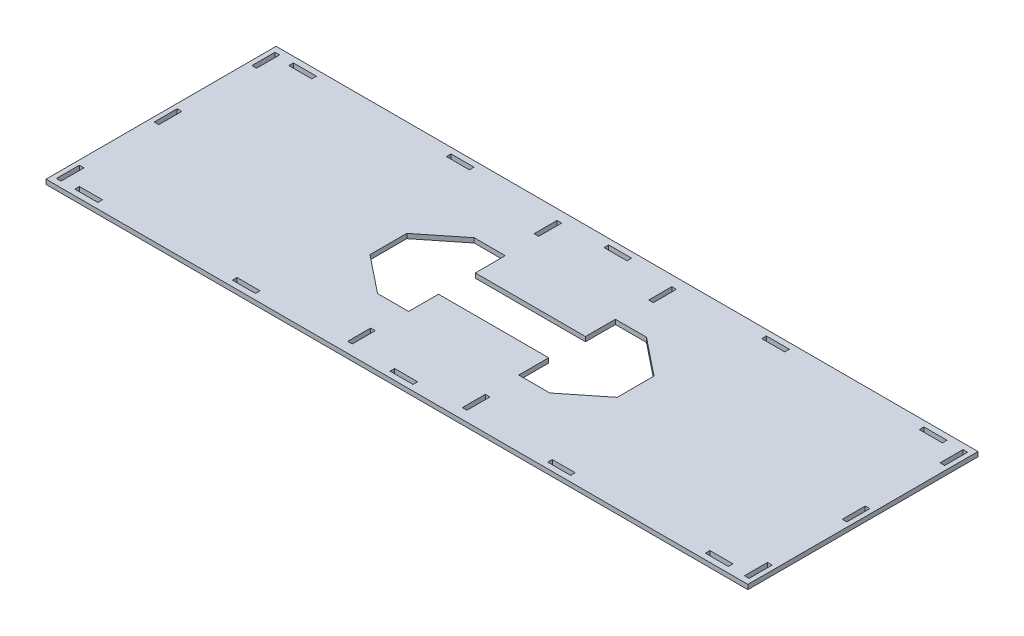
SolidWorks part; units mm, degrees
ref_plane "Front Plane" through (0, 0, 0) normal (0, 0, 1) x (1, 0, 0)
ref_plane "Top Plane" through (0, 0, 0) normal (0, 1, 0) x (1, 0, 0)
ref_plane "Right Plane" through (0, 0, 0) normal (1, 0, 0) x (0, 0, -1)
sketch "Sketch1" plane through (0, 0, 0) normal (0, 1, 0) x (1, 0, 0)
  line L0 (0, 0) -> (0, 189.2154) construction
  line L1 (-305, 100) -> (-305, -100)
  line L2 (-305, -100) -> (305, -100)
  line L4 (-305, 100) -> (305, 100)
  line L6 (-330, -100) -> (330, 100) construction
  line L7 (-330, 100) -> (330, -100) construction
  line L60 (-301, -95) -> (-301, -75)
  line L61 (-301, -95) -> (326, -95) construction
  line L62 (-301, -95) -> (-301, 95) construction
  line L63 (-301, 95) -> (326, 95) construction
  line L65 (-301, -95) -> (326, 95) construction
  line L66 (-301, 95) -> (326, -95) construction
  line L67 (-301, -95) -> (-297, -95)
  line L68 (-301, 95) -> (-297, 95)
  line L69 (-301, -75) -> (-297, -75)
  line L71 (-421.8057, 0) -> (404.5887, 0) construction
  line L72 (-301, 75) -> (-301, 95)
  line L73 (-301, -10) -> (-297, -10)
  line L76 (-301, -10) -> (-301, 10)
  line L77 (-301, 10) -> (-297, 10)
  line L78 (-297, 10) -> (-297, -10)
  line L79 (-301, 75) -> (-297, 75)
  line L91 (-265, 95) -> (-285, 95)
  line L93 (-265, 95) -> (-265, 91)
  line L94 (-148, 95) -> (-128, 95)
  line L95 (-148, 95) -> (-148, 91)
  line L96 (-128, 95) -> (-128, 91)
  line L97 (9, 95) -> (9, 91)
  line L98 (-11, 95) -> (-11, 91)
  line L99 (-265, 91) -> (-285, 91)
  line L100 (-148, 91) -> (-128, 91)
  line L101 (9, 91) -> (-11, 91)
  line L104 (9, 95) -> (-11, 95)
  line L128 (9, -95) -> (-11, -95)
  line L129 (9, -95) -> (9, -91)
  line L131 (-11, -95) -> (-11, -91)
  line L132 (-148, -95) -> (-148, -91)
  line L133 (-148, -91) -> (-128, -91)
  line L134 (-128, -95) -> (-128, -91)
  line L135 (-148, -95) -> (-128, -95)
  line L136 (-265, -95) -> (-265, -91)
  line L137 (-265, -91) -> (-285, -91)
  line L139 (-265, -95) -> (-285, -95)
  line L143 (-74.8597, -12) -> (-74.8597, 12) construction
  line L144 (-74.8597, 0) -> (0, 0) construction
  line L145 (-47.8597, -91) -> (-47.8597, -71)
  line L147 (-51.8597, -91) -> (-51.8597, -71)
  line L148 (-47.8597, -71) -> (-51.8597, -71)
  line L149 (-51.8597, -42) -> (-51.8597, -22)
  line L150 (-51.8597, -42) -> (-47.8597, -42)
  line L151 (-47.8597, -42) -> (-47.8597, -22)
  line L152 (-51.8597, -22) -> (-47.8597, -22)
  line L161 (-74.8597, -16) -> (-74.8597, -12)
  line L162 (-74.8597, -16) -> (-54.8597, -16)
  line L163 (-54.8597, -16) -> (-54.8597, -12)
  line L164 (-74.8597, -12) -> (-54.8597, -12)
  line L165 (-74.8597, 12) -> (-74.8597, 16)
  line L166 (-74.8597, 12) -> (-54.8597, 12)
  line L167 (-54.8597, 12) -> (-54.8597, 16)
  line L168 (-74.8597, 16) -> (-54.8597, 16)
  line L169 (-51.8597, 22) -> (-51.8597, 42)
  line L170 (-51.8597, 22) -> (-47.8597, 22)
  line L171 (-47.8597, 22) -> (-47.8597, 42)
  line L172 (-51.8597, 42) -> (-47.8597, 42)
  line L177 (-10, -16) -> (-10, -12)
  line L178 (-10, -16) -> (10, -16)
  line L179 (10, -16) -> (10, -12)
  line L180 (-10, -12) -> (10, -12)
  line L181 (-9.8597, 12) -> (-9.8597, 16)
  line L182 (-9.8597, 12) -> (10.1403, 12)
  line L183 (10.1403, 12) -> (10.1403, 16)
  line L184 (-9.8597, 16) -> (10.1403, 16)
  line L201 (305, 100) -> (305, -100)
  line L202 (-297, 189.2154) -> (-297, -166.9381) construction
  line L204 (-285, 95) -> (-285, 91)
  line L205 (-297, 75) -> (-297, 95)
  line L206 (-285, -91) -> (-285, -95)
  line L208 (-297, -75) -> (-297, -95)
  line L210 (126, 95) -> (126, 91)
  line L211 (126, 91) -> (146, 91)
  line L212 (146, 91) -> (146, 95)
  line L213 (146, 95) -> (126, 95)
  line L214 (263, 95) -> (263, 91)
  line L215 (263, 91) -> (283, 91)
  line L216 (283, 91) -> (283, 95)
  line L222 (263, 95) -> (283, 95)
  line L223 (-51.8597, -91) -> (-47.8597, -91)
  line L224 (9, -91) -> (-11, -91)
  line L225 (51.8597, -91) -> (47.8597, -91)
  line L226 (47.8597, -91) -> (47.8597, -71)
  line L227 (47.8597, -71) -> (51.8597, -71)
  line L228 (51.8597, -91) -> (51.8597, -71)
  line L229 (51.8597, -42) -> (47.8597, -42)
  line L230 (47.8597, -42) -> (47.8597, -22)
  line L231 (51.8597, -22) -> (47.8597, -22)
  line L232 (51.8597, -42) -> (51.8597, -22)
  line L233 (74.8597, -16) -> (54.8597, -16)
  line L234 (54.8597, -16) -> (54.8597, -12)
  line L235 (74.8597, -12) -> (54.8597, -12)
  line L236 (74.8597, -16) -> (74.8597, -12)
  line L237 (74.8597, 12) -> (54.8597, 12)
  line L238 (54.8597, 12) -> (54.8597, 16)
  line L239 (74.8597, 16) -> (54.8597, 16)
  line L240 (74.8597, 12) -> (74.8597, 16)
  line L241 (51.8597, 22) -> (47.8597, 22)
  line L242 (47.8597, 22) -> (47.8597, 42)
  line L243 (51.8597, 42) -> (47.8597, 42)
  line L244 (51.8597, 22) -> (51.8597, 42)
  line L245 (263, -95) -> (263, -91)
  line L246 (263, -91) -> (283, -91)
  line L247 (283, -91) -> (283, -95)
  line L248 (263, -95) -> (283, -95)
  line L249 (146, -91) -> (146, -95)
  line L250 (126, -91) -> (146, -91)
  line L251 (126, -95) -> (126, -91)
  line L252 (146, -95) -> (126, -95)
  line L253 (51.8597, 91) -> (51.8597, 71)
  line L254 (47.8597, 71) -> (51.8597, 71)
  line L255 (47.8597, 91) -> (47.8597, 71)
  line L256 (51.8597, 91) -> (47.8597, 91)
  line L257 (-51.8597, 91) -> (-47.8597, 91)
  line L258 (-47.8597, 91) -> (-47.8597, 71)
  line L259 (-47.8597, 71) -> (-51.8597, 71)
  line L260 (-51.8597, 91) -> (-51.8597, 71)
  line L261 (301, 75) -> (297, 75)
  line L262 (301, 75) -> (301, 95)
  line L263 (301, 95) -> (297, 95)
  line L264 (297, 75) -> (297, 95)
  line L265 (301, -10) -> (301, 10)
  line L266 (301, 10) -> (297, 10)
  line L267 (297, 10) -> (297, -10)
  line L268 (301, -10) -> (297, -10)
  line L269 (301, -75) -> (297, -75)
  line L270 (301, -95) -> (301, -75)
  line L271 (301, -95) -> (297, -95)
  line L272 (297, -75) -> (297, -95)
  point P63 (-299, -95)
  dimension "D2" = 200
  dimension "D3" = 8
  dimension "D4" = 190
  dimension "D5" = 20
  dimension "D6" = 20
  dimension "D7" = 20
  dimension "D8" = 10
  dimension "D9" = 20
  dimension "D10" = 5
  dimension "D11" = 20
  dimension "D12" = 20
  dimension "D13" = 610
  dimension "D14" = 117
  dimension "D15" = 117
  dimension "D16" = 20
  dimension "D17" = 4
  dimension "D18" = 4
  dimension "D19" = 4
  dimension "D20" = 117
  dimension "D21" = 20
  dimension "D22" = 117
  dimension "D23" = 20
  dimension "D24" = 4
  dimension "D25" = 253.1403
  dimension "D26" = 20
  dimension "D27" = 9
  dimension "D28" = 20
  dimension "D29" = 29
extrude "Boss-Extrude1" add sketch "Sketch1" along normal blind 4
sketch "Sketch2" plane through (0, 4, 0) normal (0, 1, 0) x (1, 0, 0)
  line L0 (-140.2913, 0) -> (187.8269, 0) construction
  line L1 (-47.8597, 16) -> (47.8597, 16)
  line L2 (-47.8597, 16) -> (-47.8597, 42)
  line L3 (-47.8597, 42) -> (-74.8597, 42)
  line L4 (-74.8597, 42) -> (-107.4192, 16)
  line L5 (-107.4192, 16) -> (-107.4192, -16)
  line L6 (0, 51.589) -> (0, -41.6401) construction
  line L7 (-74.8597, -42) -> (-107.4192, -16)
  line L8 (-47.8597, -42) -> (-74.8597, -42)
  line L9 (-47.8597, -16) -> (-47.8597, -42)
  line L10 (-47.8597, -16) -> (47.8597, -16)
  line L11 (47.8597, -42) -> (74.8597, -42)
  line L12 (74.8597, -42) -> (107.4192, -16)
  line L13 (107.4192, 16) -> (107.4192, -16)
  line L14 (74.8597, 42) -> (107.4192, 16)
  line L15 (47.8597, 42) -> (74.8597, 42)
  line L16 (47.8597, 16) -> (47.8597, 42)
  line L17 (47.8597, -16) -> (47.8597, -42)
  point P11 (-61.3597, -42)
  point P13 (-61.3597, 42)
  point P16 (-107.4192, 0)
extrude "Cut-Extrude1" cut sketch "Sketch2" against normal blind 10
